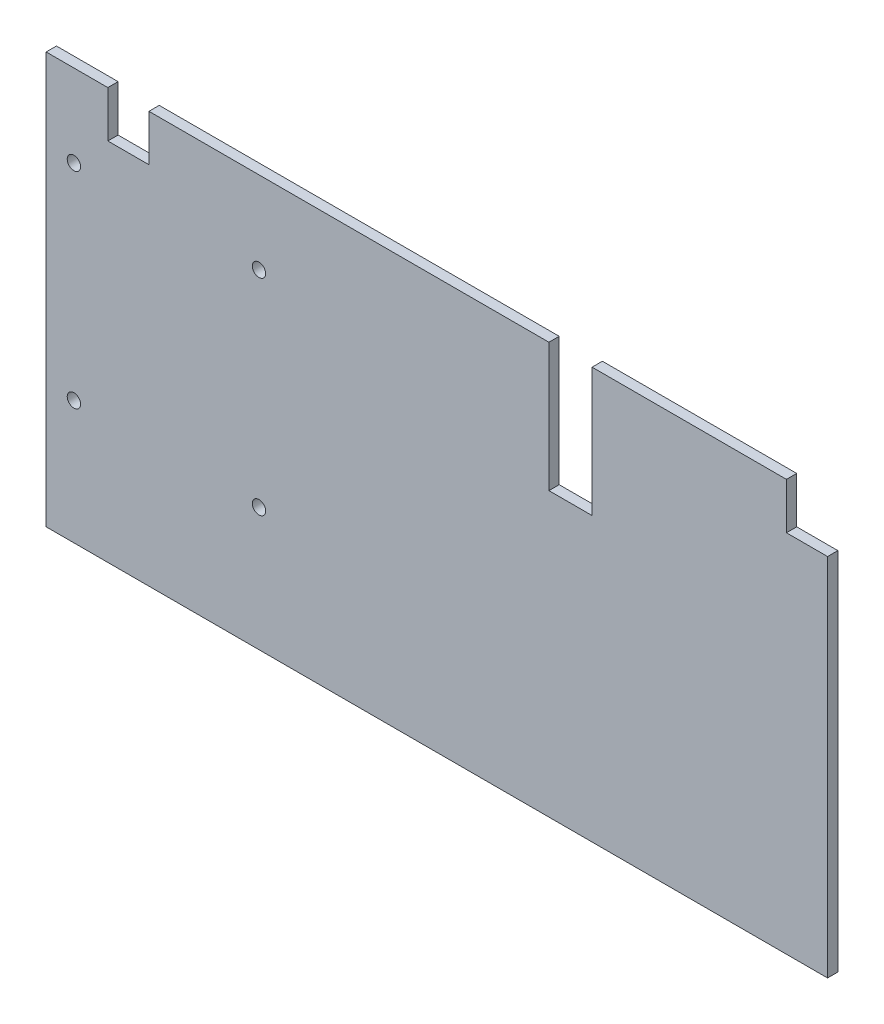
SolidWorks part; units mm, degrees
material "1.0545 (S355N)"
ref_plane "Front Plane" through (0, 0, 0) normal (0, 0, 1) x (1, 0, 0)
ref_plane "Top Plane" through (0, 0, 0) normal (0, 1, 0) x (1, 0, 0)
ref_plane "Right Plane" through (0, 0, 0) normal (1, 0, 0) x (0, 0, -1)
sketch "Sketch1" plane through (0, 0, 0) normal (0, 0, 1) x (1, 0, 0)
  line L0 (0, 460.58) -> (0, -350.58) construction
  line L5 (-393, 300.7391) -> (-393, -210.0403) construction
  line L6 (-21, 55) -> (21, 55)
  line L7 (0, 0) -> (-447.8579, 0) construction
  line L8 (-21, 55) -> (-21, 180)
  line L9 (-21, 180) -> (-410, 180)
  line L10 (21, 55) -> (21, 180)
  line L11 (21, 180) -> (210, 180)
  line L12 (210, 180) -> (210, 135)
  line L13 (210, 135) -> (250, 135)
  line L14 (250, 135) -> (250, -220)
  line L15 (-410, 180) -> (-410, 135)
  line L16 (-410, 135) -> (-450, 135)
  line L17 (-510, 180) -> (-510, -220)
  line L18 (-510, -220) -> (250, -220)
  line L19 (-450, 135) -> (-450, 180)
  line L20 (-450, 180) -> (-510, 180)
  circle A0 centre (-303, 100) radius 6.5
  circle A1 centre (-483, 100) radius 6.5
  circle A2 centre (-303, -100) radius 6.5
  circle A3 centre (-483, -100) radius 6.5
  point P7 (0, 55)
  point P29 (-513.2908, 180)
  dimension "D12" = 13
  dimension "D13" = 400
  dimension "D1" = 393
  dimension "D2" = 42
  dimension "D3" = 55
  dimension "D4" = 125
  dimension "D5" = 40
  dimension "D6" = 45
  dimension "D7" = 189
  dimension "D8" = 660
  dimension "D9" = 45
  dimension "D10" = 90
  dimension "D11" = 100
  dimension "D14" = 40
  dimension "D15" = 760
extrude "Boss-Extrude1" add sketch "Sketch1" along normal blind 10
